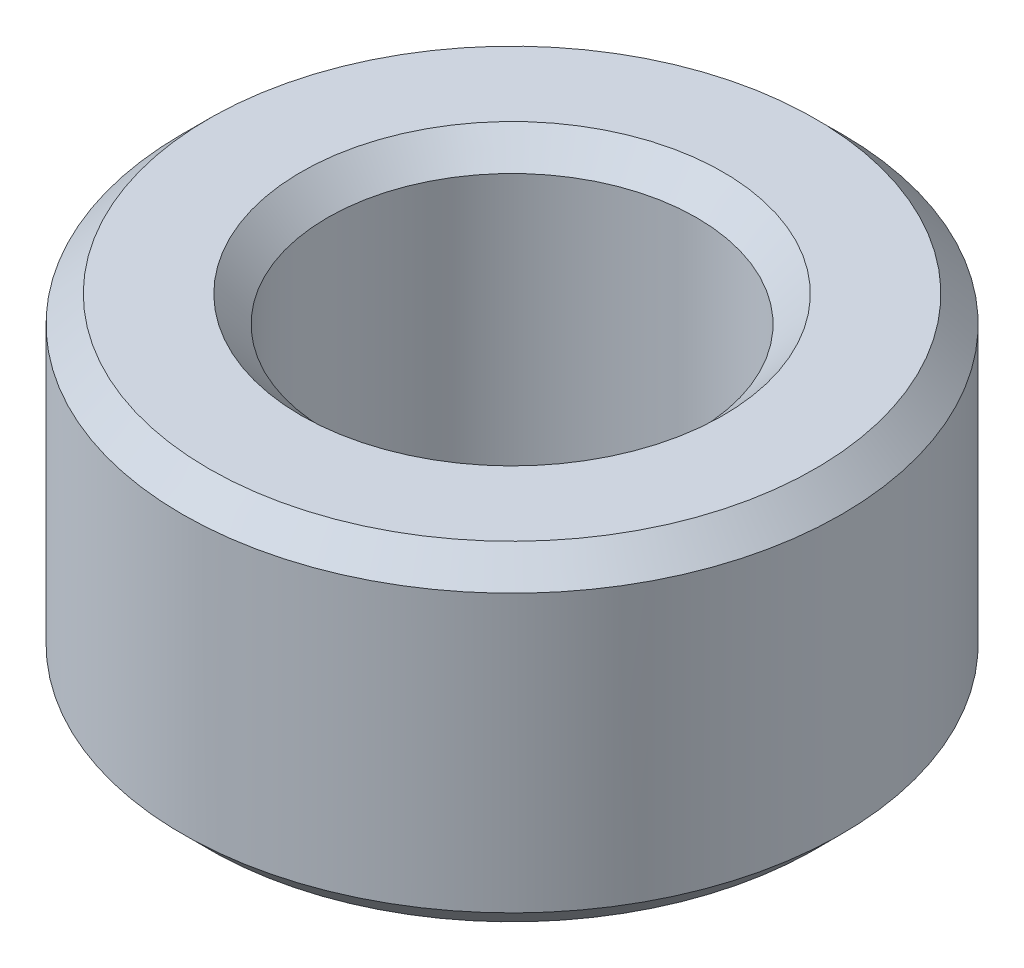
SolidWorks part; units mm, degrees
ref_plane "Front Plane" through (0, 0, 0) normal (0, 0, 1) x (1, 0, 0)
ref_plane "Top Plane" through (0, 0, 0) normal (0, 1, 0) x (1, 0, 0)
ref_plane "Right Plane" through (0, 0, 0) normal (1, 0, 0) x (0, 0, -1)
sketch "Sketch1" plane through (0, 0, 0) normal (0, 0, 1) x (1, 0, 0)
  line L0 (0, 0) -> (0, 1.3501) construction
  line L1 (1.778, 1.5875) -> (3.175, 1.5875)
  line L2 (3.175, 1.5875) -> (3.175, -1.5875)
  line L3 (3.175, -1.5875) -> (1.778, -1.5875)
  line L4 (1.778, -1.5875) -> (1.778, 1.5875)
  point P6 (1.778, 0)
  dimension "D1" = 3.556
  dimension "D2" = 6.35
  dimension "D3" = 3.175
revolve "Revolve1" add sketch "Sketch1" angle 360 about L0
chamfer "Chamfer1" distance 0.254 angle 45 4 edges at (0, -1.5875, -3.175) (0, 1.5875, -3.175) (0, 1.5875, -1.778) (0, -1.5875, -1.778)
